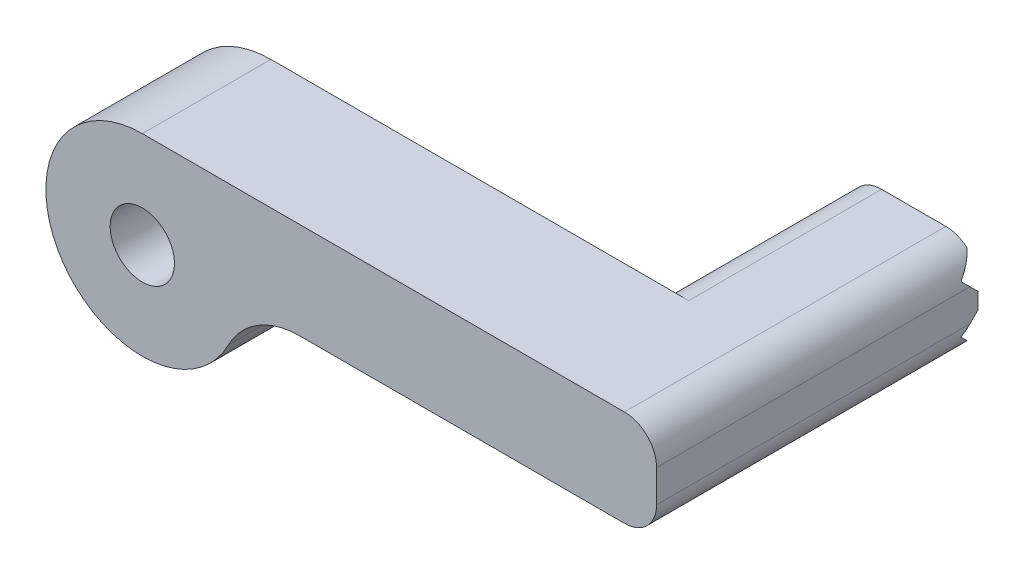
SolidWorks part; units mm, degrees
ref_plane "Front Plane" through (0, 0, 0) normal (0, 0, 1) x (1, 0, 0)
ref_plane "Top Plane" through (0, 0, 0) normal (0, 1, 0) x (1, 0, 0)
ref_plane "Right Plane" through (0, 0, 0) normal (1, 0, 0) x (0, 0, -1)
sketch "Sketch1" plane through (0, 0, 0) normal (0, 0, 1) x (1, 0, 0)
  line L0 (-23.3162, 68.9712) -> (-23.3162, 70.9712)
  line L1 (-23.3162, 70.9712) -> (-55.3162, 70.9712)
  line L2 (-31.3162, 70.9712) -> (-31.3162, 64.9712)
  line L3 (-23.3162, 64.9712) -> (-23.3162, 68.9712)
  line L4 (-45.5183, 64.9712) -> (-23.3162, 64.9712)
  line L5 (-32.8162, 67.9712) -> (-31.3162, 67.9712)
  arc A0 (-49.9719, 62.2439) -> (-45.5183, 64.9712) centre (-45.5183, 59.9712) cw
  arc A1 (-55.3162, 70.9712) -> (-49.9719, 62.2439) centre (-55.3162, 64.9712) ccw
  arc A2 (-32.8162, 67.9712) -> (-32.8162, 64.9712) centre (-32.8162, 66.4712) ccw
  dimension "D1" = 5
  dimension "D2" = 2
  dimension "D3" = 8
  dimension "D4" = 32
extrude "Boss-Extrude1" add sketch "Sketch1" along normal blind 8 contours L1 A1 A0 L4 L3 L0
sketch "Sketch2" plane through (0, 0, 0) normal (0, 0, 1) x (1, 0, 0)
  line L0 (-23.3162, 68.9712) -> (-23.3162, 70.9712)
  line L1 (-23.3162, 70.9712) -> (-31.3162, 70.9712)
  line L2 (-31.3162, 70.9712) -> (-31.3162, 67.9712)
  line L3 (-23.3162, 64.9712) -> (-23.3162, 68.9712)
  line L4 (-31.3162, 64.9712) -> (-23.3162, 64.9712)
  line L6 (-31.3162, 67.9712) -> (-31.3162, 64.9712)
  dimension "D2" = 2
  dimension "D3" = 8
extrude "Boss-Extrude2" add sketch "Sketch2" against normal blind 12
sketch "Sketch3" plane through (0, 0, 0) normal (0, 0, -1) x (-1, 0, 0)
  circle A0 centre (55.3162, 64.9712) radius 2
extrude "Cut-Extrude1" cut sketch "Sketch3" against normal blind 8
fillet "Fillet1" radius 2 4 edges at (-23.3162, 64.9712, -2) (-23.3162, 70.9712, -2)
sketch "Sketch4" plane through (-31.3162, 0, 0) normal (-1, 0, 0) x (0, 0, 1)
  line L0 (-12, 70.9712) -> (-13, 70.9712)
  line L1 (-13, 70.9712) -> (-13, 64.9712)
  line L2 (-12, 65.4712) -> (-12, 64.9712)
  line L3 (-12, 70.9712) -> (-12, 70.4712)
  line L4 (-12, 70.4712) -> (-11, 69.4712)
  line L5 (-11, 69.4712) -> (-12, 68.4712)
  line L6 (-12, 65.4712) -> (-11, 66.4712)
  line L7 (-11, 66.4712) -> (-12, 67.4712)
  line L8 (-12, 67.4712) -> (-12, 68.4712)
  line L9 (-13, 64.9712) -> (-12, 64.9712)
  line L11 (-12, 68.9712) -> (-12, 66.9712) construction
extrude "Cut-Extrude2" cut sketch "Sketch4" against normal blind 8
